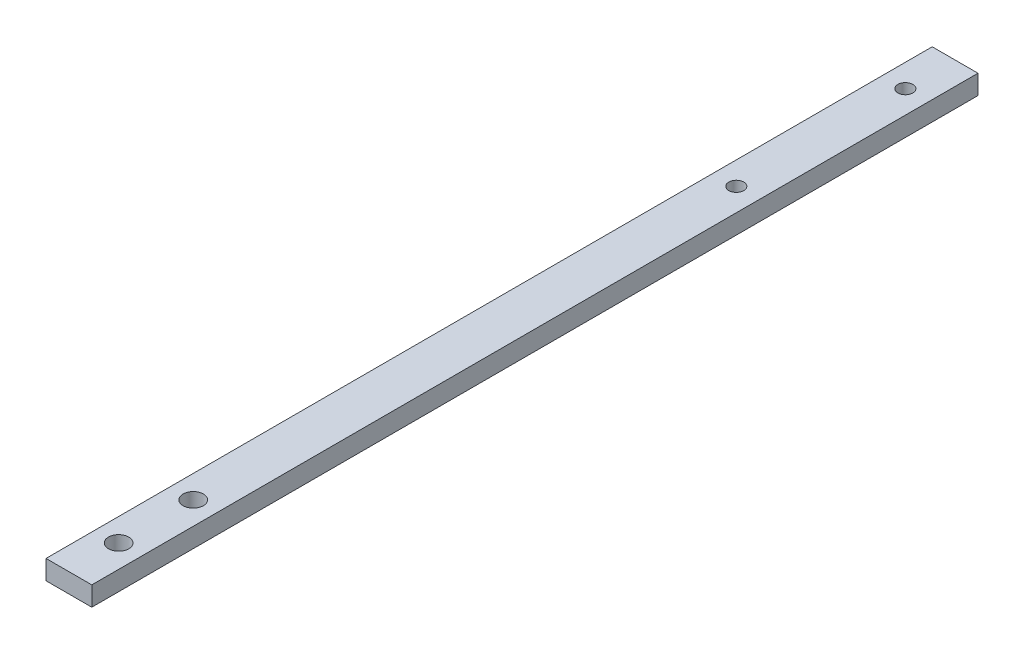
SolidWorks part; units mm, degrees
ref_plane "Front Plane" through (0, 0, 0) normal (0, 0, 1) x (1, 0, 0)
ref_plane "Top Plane" through (0, 0, 0) normal (0, 1, 0) x (1, 0, 0)
ref_plane "Right Plane" through (0, 0, 0) normal (1, 0, 0) x (0, 0, -1)
sketch "Sketch1" plane through (0, 0, 0) normal (0, 0, 1) x (1, 0, 0)
  circle A0 centre (0, 0) radius 2.5
  dimension "D1" = 5
extrude "Boss-Extrude1" add sketch "Sketch1" along normal blind 56
sketch "Sketch2" plane through (0, 0, 56) normal (0, 0, 1) x (1, 0, 0)
  line L1 (2.3024, -0.9741) -> (-2.3024, -0.9741)
  line L2 (2.3024, -0.9741) -> (2.3024, 0.9741)
  line L3 (2.3024, 0.9741) -> (-2.3024, 0.9741)
  line L4 (-2.3024, -0.9741) -> (-2.3024, 0.9741)
  line L5 (2.3024, -0.9741) -> (-2.3024, 0.9741) construction
  line L6 (2.3024, 0.9741) -> (-2.3024, -0.9741) construction
  circle A0 centre (0, 0) radius 2.5 construction
  point P0 (0, 0)
extrude "Boss-Extrude2" add sketch "Sketch2" along normal blind 33.1
sketch "Sketch3" plane through (0, 0.9741, 0) normal (0, 1, 0) x (1, 0, 0)
  line L0 (2.3024, -89.1) -> (-2.3024, -89.1) construction
  circle A0 centre (0, -76.6) radius 1.0227
  circle A1 centre (0, -84.1) radius 1.0227
  point P6 (0, -89.1)
  dimension "D1" = 5
  dimension "D2" = 12.5
extrude "Cut-Extrude1" cut sketch "Sketch3" against normal through all
sketch "Sketch4" plane through (0, 0, 0) normal (0, 1, 0) x (1, 0, 0)
  line L0 (0, 0) -> (0, -14.2164) construction
  line L1 (2.5, 0) -> (-2.5, 0) construction
  circle A0 centre (0, -5) radius 0.75
  circle A1 centre (0, -22) radius 0.75
  dimension "D1" = 1.5
  dimension "D2" = 1.5
  dimension "D3" = 17
  dimension "D4" = 5
extrude "Cut-Extrude2" cut sketch "Sketch4" against normal through all and the other way through all
sketch "Sketch5" plane through (0, 0, 89.1) normal (0, 0, 1) x (1, 0, 0)
  line L1 (-2.3024, 0.9741) -> (2.3024, 0.9741)
  line L2 (-2.3024, 0.9741) -> (-2.3024, -0.9741)
  line L3 (-2.3024, -0.9741) -> (2.3024, -0.9741)
  line L4 (2.3024, 0.9741) -> (2.3024, -0.9741)
extrude "Cut-Extrude3" cut sketch "Sketch5" against normal through all flip side to cut
